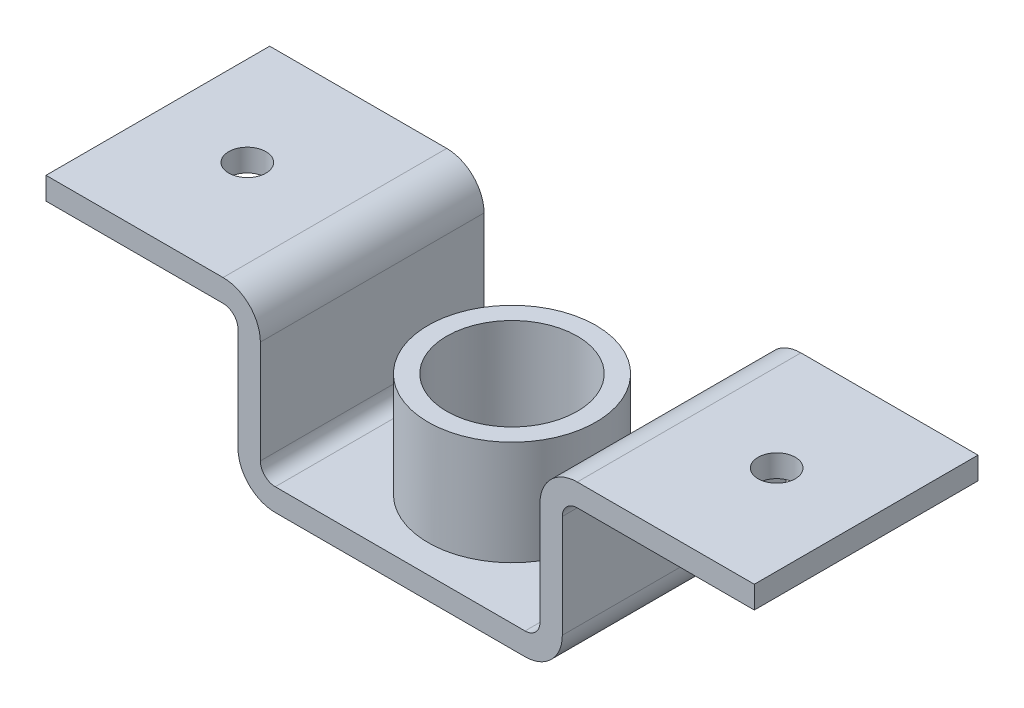
SolidWorks part; units mm, degrees
ref_plane "Front Plane" through (0, 0, 0) normal (0, 0, 1) x (1, 0, 0)
ref_plane "Top Plane" through (0, 0, 0) normal (0, 1, 0) x (1, 0, 0)
ref_plane "Right Plane" through (0, 0, 0) normal (1, 0, 0) x (0, 0, -1)
sketch "Sketch1" plane through (0, 0, 0) normal (0, 0, 1) x (1, 0, 0)
  line L0 (0, 0) -> (0, 873.8219) construction
  line L1 (-167.5, 0) -> (167.5, 0)
  line L2 (217.5, 50) -> (217.5, 188)
  line L3 (237.5, 208) -> (475, 208)
  line L4 (475, 208) -> (475, 238)
  line L5 (475, 238) -> (237.5, 238)
  line L6 (187.5, 188) -> (187.5, 50)
  line L7 (167.5, 30) -> (-167.5, 30)
  line L8 (-187.5, 50) -> (-187.5, 188)
  line L9 (-237.5, 238) -> (-475, 238)
  line L10 (-475, 238) -> (-475, 208)
  line L11 (-475, 208) -> (-237.5, 208)
  line L12 (-217.5, 188) -> (-217.5, 50)
  arc A0 (187.5, 50) -> (167.5, 30) centre (167.5, 50) cw
  arc A1 (-167.5, 30) -> (-187.5, 50) centre (-167.5, 50) cw
  arc A2 (167.5, 0) -> (217.5, 50) centre (167.5, 50) ccw
  arc A3 (-167.5, 0) -> (-217.5, 50) centre (-167.5, 50) cw
  arc A4 (237.5, 238) -> (187.5, 188) centre (237.5, 188) ccw
  arc A5 (-187.5, 188) -> (-237.5, 238) centre (-237.5, 188) ccw
  arc A6 (217.5, 188) -> (237.5, 208) centre (237.5, 188) cw
  arc A7 (-237.5, 208) -> (-217.5, 188) centre (-237.5, 188) cw
  dimension "D7" = 20
  dimension "D8" = 50
  dimension "D9" = 50
  dimension "D10" = 20
  dimension "D1" = 950
  dimension "D2" = 375
  dimension "D3" = 30
  dimension "D4" = 30
  dimension "D5" = 238
  dimension "D6" = 30
extrude "Boss-Extrude1" add sketch "Sketch1" along normal blind 300
sketch "Sketch2" plane through (0, 0, 0) normal (0, 1, 0) x (1, 0, 0)
  line L0 (-237.5, -300) -> (-475, -300) construction
  circle A0 centre (0, -150) radius 112.5
  circle A1 centre (0, -150) radius 87.5
  dimension "D1" = 225
  dimension "D3" = 175
  dimension "D2" = 150
extrude "Boss-Extrude2" add sketch "Sketch2" along normal blind 170
sketch "Sketch3" plane through (0, 0, 0) normal (0, 1, 0) x (1, 0, 0)
  circle A0 centre (0, -150) radius 37.5
  dimension "D1" = 75
extrude "Cut-Extrude3" cut sketch "Sketch3" along normal through all
sketch "Sketch5" plane through (0, 0, 0) normal (0, 1, 0) x (1, 0, 0)
  line L0 (-237.5, -300) -> (-475, -300) construction
  line L1 (-475, -300) -> (-475, 0) construction
  line L2 (475, -300) -> (475, 0) construction
  circle A0 centre (-355, -150) radius 25
  circle A1 centre (355, -150) radius 25
  point P4 (0, 0)
  dimension "D1" = 50
  dimension "D2" = 150
  dimension "D3" = 120
  dimension "D4" = 120
extrude "Cut-Extrude4" cut sketch "Sketch5" along normal through all from surface at 208 starting at face at (-356.25, 208, 150)
